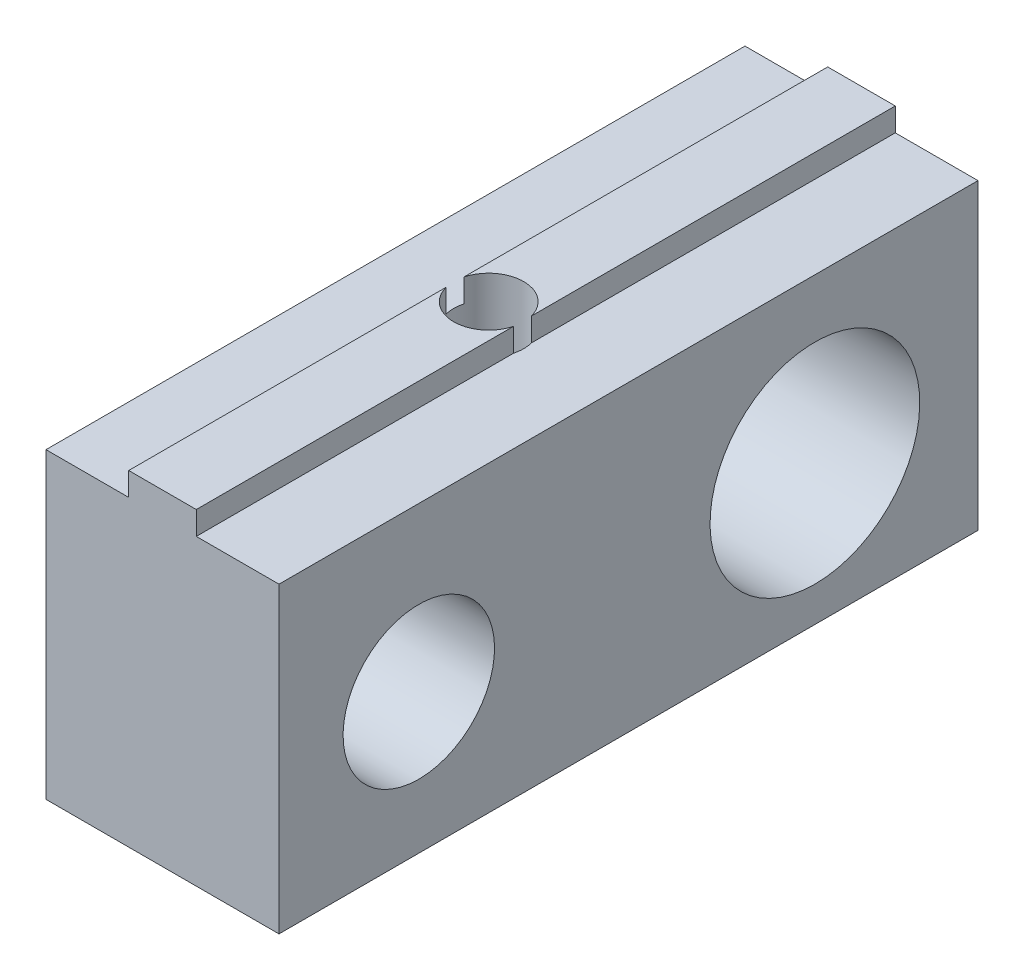
SolidWorks part; units mm, degrees
ref_plane "Front Plane" through (0, 0, 0) normal (0, 0, 1) x (1, 0, 0)
ref_plane "Top Plane" through (0, 0, 0) normal (0, 1, 0) x (1, 0, 0)
ref_plane "Right Plane" through (0, 0, 0) normal (1, 0, 0) x (0, 0, -1)
sketch "Sketch1" plane through (0, 0, 0) normal (0, 0, 1) x (1, 0, 0)
  line L0 (-5, 0) -> (5, 0)
  line L1 (5, 0) -> (5, 1)
  line L2 (5, 1) -> (1.45, 1)
  line L3 (1.45, 1) -> (1.45, 2)
  line L4 (1.45, 2) -> (-1.45, 2)
  line L5 (-1.45, 2) -> (-1.45, 1)
  line L6 (-1.45, 1) -> (-5, 1)
  line L7 (-5, 1) -> (-5, 0)
  point P9 (0, 0)
  dimension "D1" = 10
  dimension "D2" = 2.9
  dimension "D3" = 1
  dimension "D4" = 1
extrude "MakerBeamFix" add sketch "Sketch1" along normal mid plane 30
sketch "Sketch3" plane through (-5, 0, 0) normal (-1, 0, 0) x (0, 0, 1)
  line L1 (15, -12) -> (-15, -12)
  line L2 (15, -12) -> (15, 0)
  line L3 (15, 0) -> (-15, 0)
  line L4 (-15, -12) -> (-15, 0)
  line L5 (15, -12) -> (-15, 0) construction
  line L6 (15, 0) -> (-15, -12) construction
  line L7 (-15, 1) -> (-15, 0) construction
  line L8 (-15, 2) -> (-15, 1) construction
  line L9 (15, 0) -> (-15, 0) construction
  circle A0 centre (9, -6) radius 3.25
  circle A1 centre (-8, -6) radius 4.5
  point P8 (0, -6)
  dimension "D1" = 9
  dimension "D4" = 6.5
  dimension "D3" = 12
  dimension "D5" = 6
  dimension "D6" = 7
extrude "DrillKeyAndSmallHexDriver" add sketch "Sketch3" against normal blind 10
sketch "Sketch4" plane through (0, -12, 0) normal (0, -1, 0) x (1, 0, 0)
  line L0 (-5, -15) -> (-5, 15) construction
  circle A0 centre (0, 1) radius 1.5
  point P4 (0, 1.9512)
  point P5 (-5, 0)
  dimension "D1" = 3
  dimension "D2" = 5
  dimension "D3" = 1
extrude "FixingHole" cut sketch "Sketch4" against normal through all
ref_plane "Plane1" through (0, -6, 0) normal (0, 1, 0) x (1, 0, 0)
sketch "Sketch5" plane through (0, -6, 0) normal (0, 1, 0) x (1, 0, 0)
  circle A0 centre (0, -1) radius 4.25
  circle A1 centre (0, -1) radius 1.5 construction
  dimension "D1" = 8.5
extrude "DriverHole" cut sketch "Sketch5" against normal through all
